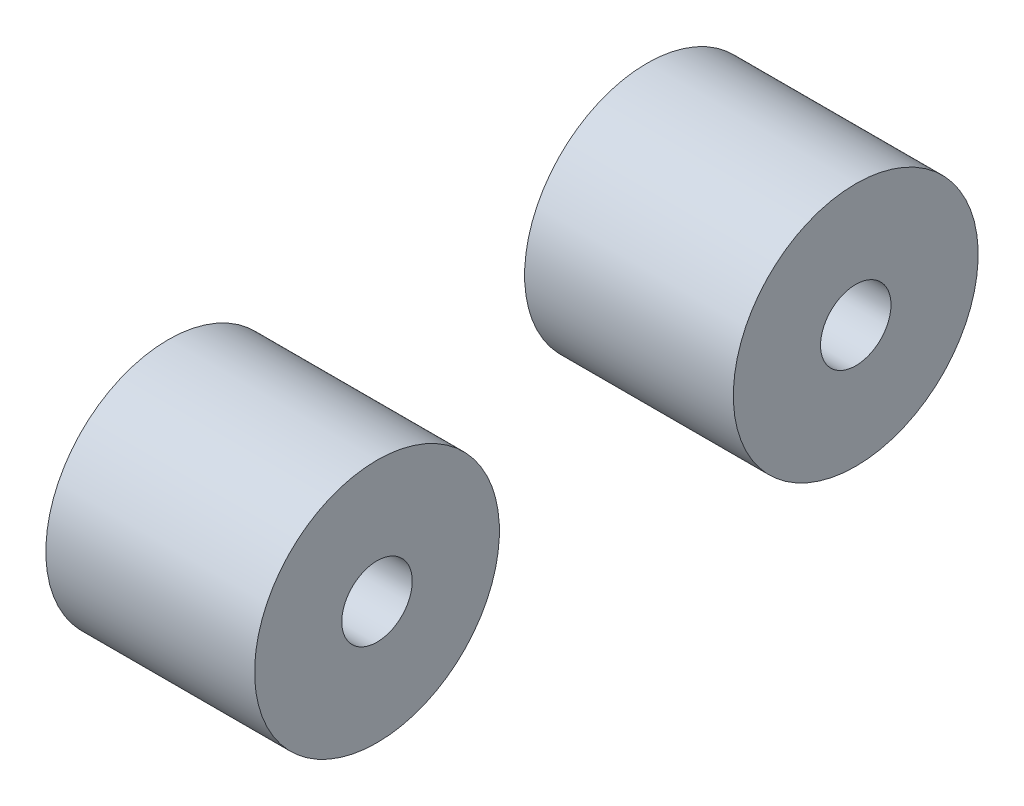
SolidWorks part; units mm, degrees
ref_plane "Front Plane" through (0, 0, 0) normal (0, 0, 1) x (1, 0, 0)
ref_plane "Top Plane" through (0, 0, 0) normal (0, 1, 0) x (1, 0, 0)
ref_plane "Right Plane" through (0, 0, 0) normal (1, 0, 0) x (0, 0, -1)
sketch "Sketch1" plane through (0, 0, 0) normal (0, 0, 1) x (1, 0, 0)
  line L0 (8.255, 0) -> (-8.255, 0) construction
  line L1 (30.255, 0) -> (-30.255, 0) construction
  line L2 (8.255, 0) -> (8.255, 12.9)
  line L3 (8.255, 12.9) -> (30.255, 12.9)
  line L4 (30.255, 12.9) -> (30.255, 0)
  line L5 (8.255, 0) -> (30.255, 0)
  point P4 (0, 0)
  point P8 (0, 0)
  dimension "D1" = 22
  dimension "D2" = 16.51
  dimension "D3" = 12.9
revolve "Revolve1" add sketch "Sketch1" angle 360 about L5
sketch "Sketch2" plane through (8.255, 0, 0) normal (-1, 0, 0) x (0, 0, 1)
  circle A0 centre (0, 0) radius 3.7138
  dimension "D1" = 7.4275
extrude "Cut-Extrude1" cut sketch "Sketch2" against normal blind 7.5725
sketch "Sketch3" plane through (30.255, 0, 0) normal (1, 0, 0) x (0, 0, -1)
  line L0 (-20.8953, -55) -> (-20.8953, -46.1532)
  line L1 (13.175, -55) -> (-13.175, -55) construction
  line L2 (13.175, -55) -> (13.175, 55) construction
  line L3 (13.175, 55) -> (-13.175, 55) construction
  line L4 (-13.175, -55) -> (-13.175, 55) construction
  line L5 (13.175, -55) -> (-13.175, 55) construction
  line L6 (13.175, 55) -> (-13.175, -55) construction
  line L7 (-24.3823, -32.1152) -> (-32.3245, -17.1152)
  line L9 (-5.4548, -55) -> (-5.4548, -44)
  line L11 (5.4547, -44) -> (5.4547, -55)
  line L12 (20.8953, -55) -> (20.8953, -46.1532)
  line L13 (24.3823, -32.1152) -> (32.3245, -17.1152)
  line L14 (55, 0) -> (-55, 0) construction
  line L15 (13.175, -55) -> (-13.175, 55) construction
  line L16 (13.175, 55) -> (-13.175, -55) construction
  line L17 (13.175, 55) -> (-13.175, 55) construction
  line L18 (24.3823, 32.1152) -> (32.3245, 17.1152)
  line L19 (20.8953, 55) -> (20.8953, 46.1532)
  line L20 (5.4547, 44) -> (5.4547, 55)
  line L21 (-5.4548, 55) -> (-5.4548, 44)
  line L22 (-24.3823, 32.1152) -> (-32.3245, 17.1152)
  line L23 (-20.8953, 55) -> (-20.8953, 46.1532)
  arc A15 (32.3245, -17.1152) -> (32.3245, 17.1152) centre (0, 0) ccw
  arc A16 (-5.4548, 55) -> (-20.8953, 55) centre (-13.175, 55) ccw
  arc A17 (-20.8953, -55) -> (-5.4548, -55) centre (-13.175, -55) ccw
  arc A18 (5.4547, -55) -> (20.8953, -55) centre (13.175, -55) ccw
  arc A19 (20.8953, 55) -> (5.4547, 55) centre (13.175, 55) ccw
  arc A20 (-5.4548, -44) -> (5.4547, -44) centre (0, -44) cw
  arc A21 (20.8953, -46.1532) -> (24.3823, -32.1152) centre (50.8953, -46.1532) cw
  arc A22 (-20.8953, -46.1532) -> (-24.3823, -32.1152) centre (-50.8953, -46.1532) ccw
  arc A23 (-20.8953, 46.1532) -> (-24.3823, 32.1152) centre (-50.8953, 46.1532) cw
  arc A24 (20.8953, 46.1532) -> (24.3823, 32.1152) centre (50.8953, 46.1532) ccw
  arc A25 (-5.4548, 44) -> (5.4547, 44) centre (0, 44) ccw
  arc A26 (5.4547, 55) -> (20.8953, 55) centre (13.175, 55) cw
  arc A27 (-20.8953, 55) -> (-5.4548, 55) centre (-13.175, 55) cw
  arc A29 (-32.3245, 17.1152) -> (-32.3245, -17.1152) centre (0, 0) ccw
  dimension "D3" = 15.4405
  dimension "D5" = 7.7203
  dimension "D4" = 30
  dimension "D7" = 15
  dimension "D9" = 110
  dimension "D1" = 73.152
  dimension "D6" = 15
  dimension "D2" = 26.35
  dimension "D8" = 11
sketch "Sketch4" plane through (30.255, 0, 0) normal (1, 0, 0) x (0, 0, -1)
  circle A0 centre (0, 0) radius 3.7138
  dimension "D1" = 7.4275
extrude "Cut-Extrude2" cut sketch "Sketch4" against normal blind 7.0725
move or copy body "Body-Move/Copy1" bodies to move or copy 114 copy yes number of copies 1 translate (0, 0, 50.4528)
